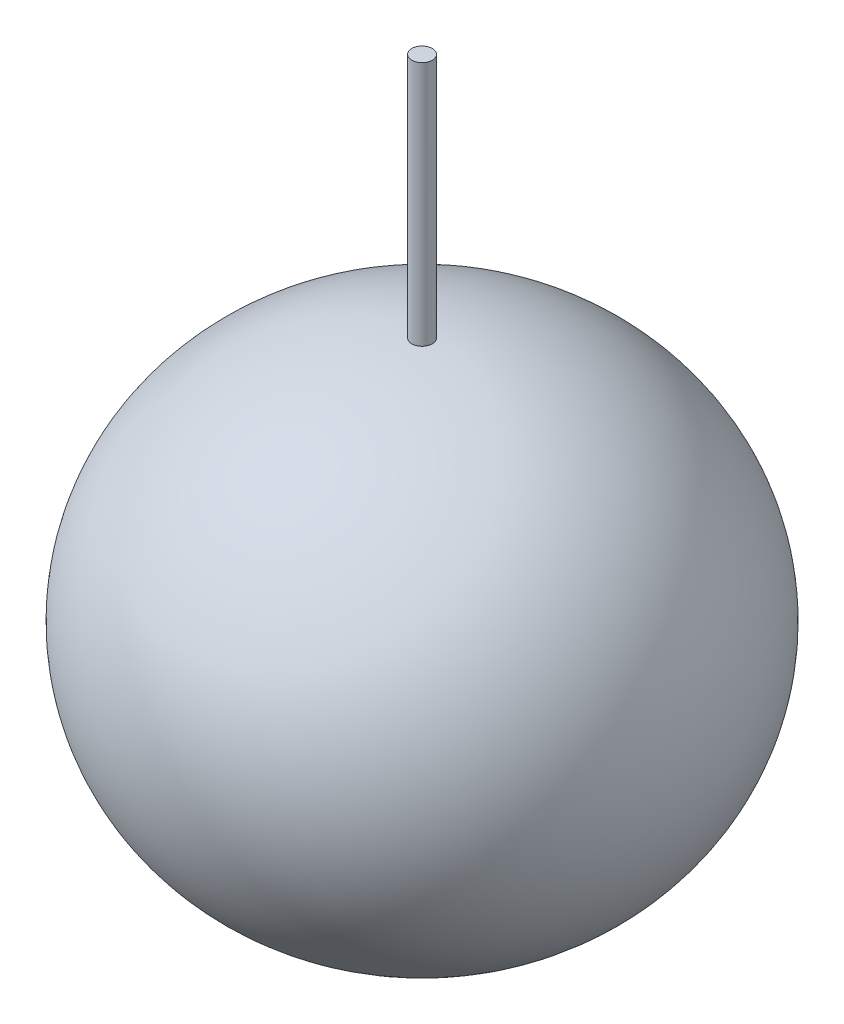
SolidWorks part; units mm, degrees
ref_plane "前视基准面" through (0, 0, 0) normal (0, 0, 1) x (1, 0, 0)
ref_plane "上视基准面" through (0, 0, 0) normal (0, 1, 0) x (1, 0, 0)
ref_plane "右视基准面" through (0, 0, 0) normal (1, 0, 0) x (0, 0, -1)
sketch "草图1" plane through (0, 0, 0) normal (0, 0, 1) x (1, 0, 0)
  line L0 (0, 30) -> (0, -30)
  line L1 (0, 0) -> (32.5, 0) construction
  ellipse E0 centre (0, 0) end of major axis (-32.5, 0) minor radius 30 (0, -30) -> (0, 30) ccw
  point P1 (0, 0)
  dimension "D1" = 60
  dimension "D2" = 65
revolve "旋转4" add sketch "草图1" angle 360 about L0
sketch "草图2" plane through (0, 0, 0) normal (0, 1, 0) x (1, 0, 0)
  circle A0 centre (0, 0) radius 1.25
  dimension "D1" = 2.5
sketch "草图3" plane through (0, 0, 0) normal (0, 0, 1) x (1, 0, 0)
  line L0 (0, 0) -> (0, 60)
  dimension "D1" = 60
sweep "扫描1" add profiles "草图2" path "草图3"
